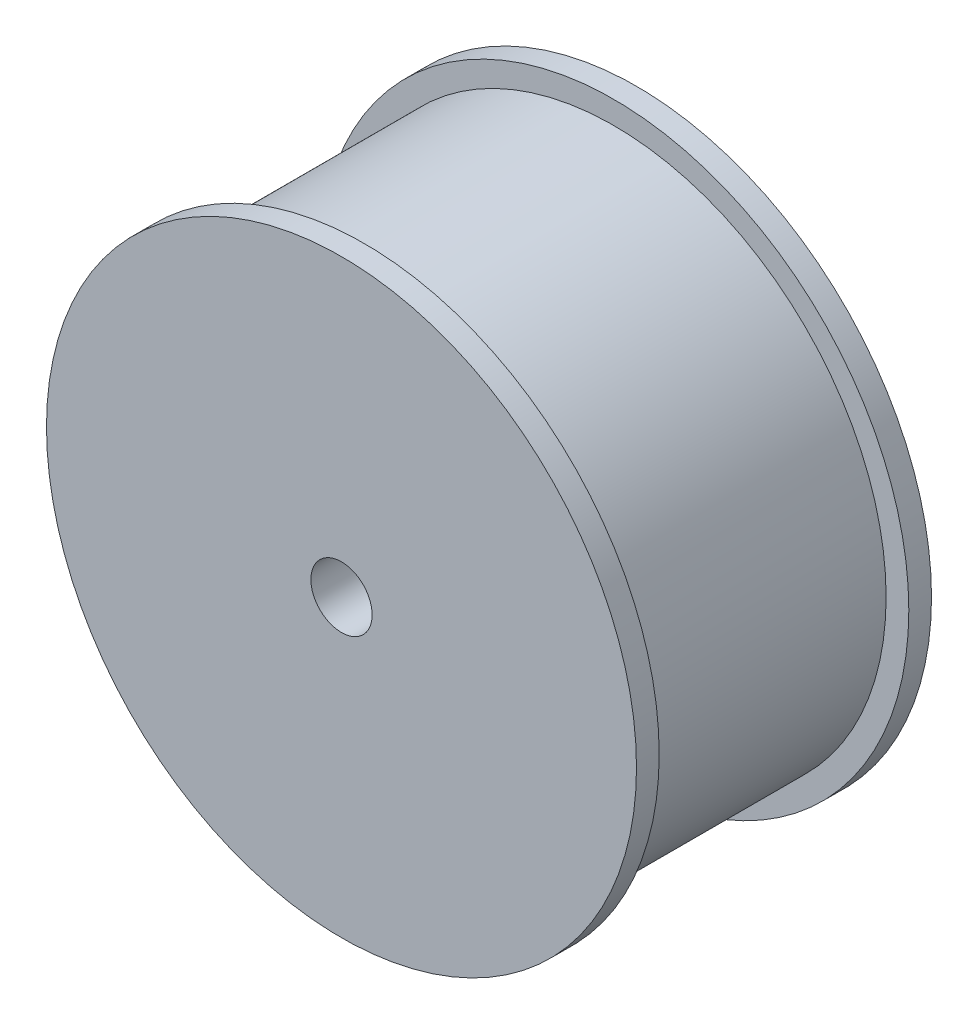
SolidWorks part; units mm, degrees
ref_plane "Front Plane" through (0, 0, 0) normal (0, 0, 1) x (1, 0, 0)
ref_plane "Top Plane" through (0, 0, 0) normal (0, 1, 0) x (1, 0, 0)
ref_plane "Right Plane" through (0, 0, 0) normal (1, 0, 0) x (0, 0, -1)
sketch "Sketch1" plane through (0, 0, 0) normal (0, 0, 1) x (1, 0, 0)
  circle A0 centre (0, 0) radius 24
  dimension "D1" = 48
extrude "Boss-Extrude1" add sketch "Sketch1" along normal mid plane 22
sketch "Sketch3" plane through (0, 0, 11) normal (0, 0, 1) x (1, 0, 0)
  circle A0 centre (0, 0) radius 26
  dimension "D1" = 52
extrude "Boss-Extrude2" add sketch "Sketch3" along normal blind 2
sketch "Sketch4" plane through (0, 0, 0) normal (0, 1, 0) x (1, 0, 0)
  line L0 (24, 0) -> (-24, 0) construction
  line L1 (24, -11) -> (24, 11) construction
  line L2 (-24, 11) -> (-24, -11) construction
  line L3 (0, 0) -> (0, 11) construction
  line L4 (24, 11) -> (-24, 11) construction
mirror "Mirror1" about plane through (0, 0, 0) normal (0, 0, 1) of "Boss-Extrude2"
sketch "Sketch5" plane through (0, 0, 13) normal (0, 0, 1) x (1, 0, 0)
  circle A0 centre (0, 0) radius 2.7
  dimension "D1" = 5.4
extrude "Cut-Extrude1" cut sketch "Sketch5" against normal through all
sketch "Sketch6" plane through (0, 0, -13) normal (0, 0, -1) x (-1, 0, 0)
  line L0 (-24, 0) -> (24, 0) construction
  circle A0 centre (0, 0) radius 6.5
  circle A1 centre (0, 0) radius 2.7
  dimension "D1" = 13
extrude "Boss-Extrude3" add sketch "Sketch6" along normal blind 4
